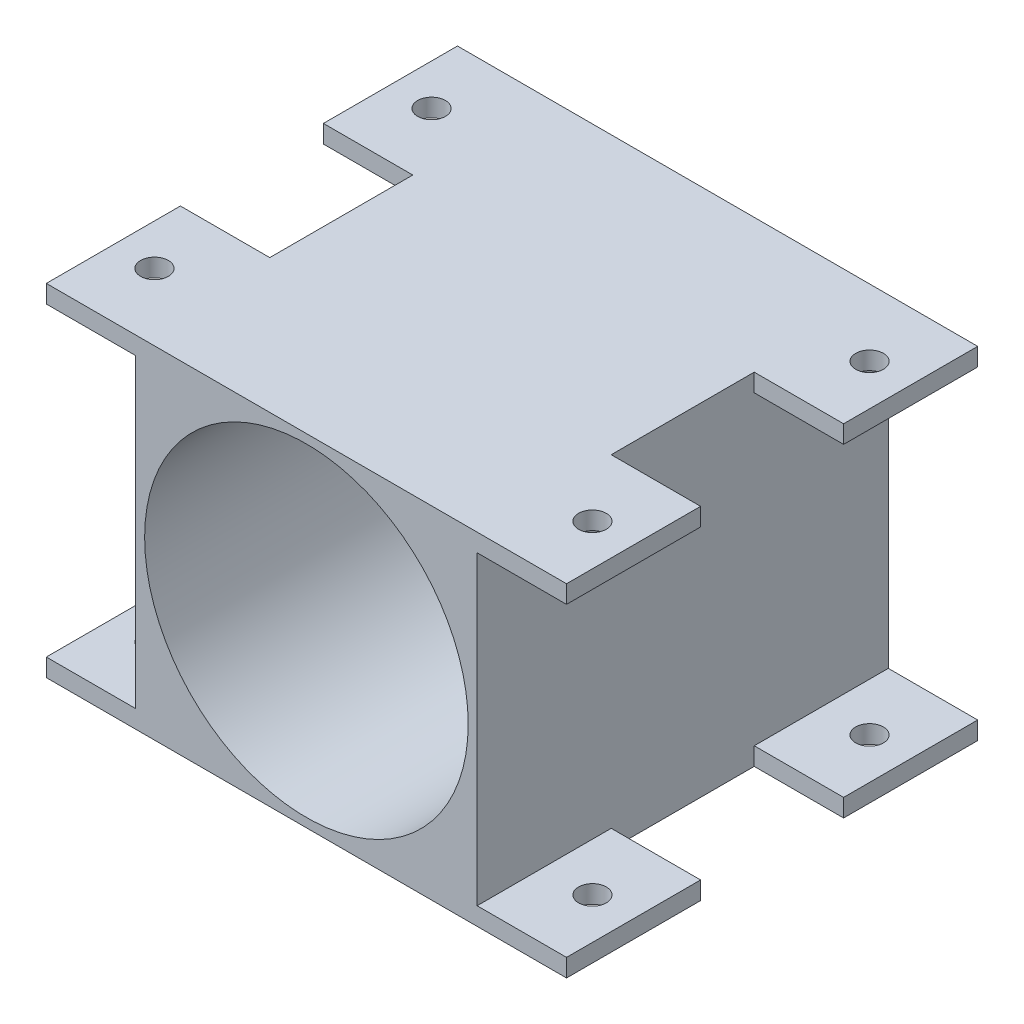
SolidWorks part; units mm, degrees
ref_plane "Front Plane" through (0, 0, 0) normal (0, 0, 1) x (1, 0, 0)
ref_plane "Top Plane" through (0, 0, 0) normal (0, 1, 0) x (1, 0, 0)
ref_plane "Right Plane" through (0, 0, 0) normal (1, 0, 0) x (0, 0, -1)
sketch "Sketch1" plane through (0, 0, 0) normal (0, 0, 1) x (1, 0, 0)
  circle A0 centre (0, 0) radius 18.1
  circle A1 centre (0, 0) radius 18.1
  circle A2 centre (-7.5, -12.9904) radius 1.55
  circle A3 centre (0, 0) radius 18.1
  circle A4 centre (7.5, -12.9904) radius 1.55
  circle A5 centre (-15, 0) radius 1.55
  circle A6 centre (0, 0) radius 18.1
  circle A7 centre (0, 6) radius 6.05
  circle A8 centre (-7.5, 12.9904) radius 1.55
  circle A9 centre (0, 0) radius 18.1
  circle A10 centre (7.5, 12.9904) radius 1.55
  circle A11 centre (0, 0) radius 18.1
  circle A12 centre (15, 0) radius 1.55
  point P24 (0, 0)
  dimension "D1" = 12.1
  dimension "D2" = 6
  dimension "D3" = 36.2
  dimension "D5" = 6
  dimension "D6" = 3.1
  dimension "D4" = 15
extrude "Boss-Extrude1" add sketch "Sketch1" along normal blind 1 contours A0 A12 A10 A8 A7 A5 A4 A2
sketch "Sketch2" plane through (0, 0, 0) normal (0, 0, -1) x (-1, 0, 0)
  line L0 (27.4238, 0) -> (-29.9497, 0) construction
  line L1 (0, 21.1091) -> (0, -19.3771) construction
  line L2 (19.1, 19.1) -> (19.1, -19.1)
  line L3 (19.1, -19.1) -> (-19.1, -19.1)
  line L4 (-19.1, 19.1) -> (-19.1, -19.1)
  line L5 (19.1, 19.1) -> (-19.1, 19.1)
  circle A1 centre (0, 0) radius 18.1 construction
  circle A2 centre (0, 0) radius 18.1
  point P9 (0, -19.1)
  point P11 (-19.1, 0)
  point P12 (19.1, 0)
  dimension "D2" = 19.1
  dimension "D1" = 19.1
extrude "Boss-Extrude2" add sketch "Sketch2" against normal blind 46
sketch "Sketch3" plane through (0, -19.1, 0) normal (0, -1, 0) x (1, 0, 0)
  line L0 (0, -11.2133) -> (0, 51.8698) construction
  line L1 (19.1, 0) -> (29.1, 0)
  line L2 (29.1, 0) -> (29.1, 15)
  line L3 (29.1, 15) -> (19.1, 15)
  line L4 (19.1, 46) -> (19.1, 0) construction
  line L5 (19.1, 46) -> (29.1, 46)
  line L6 (29.1, 46) -> (29.1, 31)
  line L7 (29.1, 31) -> (19.1, 31)
  line L8 (19.1, 31) -> (19.1, 46)
  line L9 (19.1, 15) -> (19.1, 0)
  line L10 (-19.1, 31) -> (-19.1, 46)
  line L11 (-19.1, 46) -> (-29.1, 46)
  line L12 (-29.1, 46) -> (-29.1, 31)
  line L13 (-29.1, 31) -> (-19.1, 31)
  line L14 (-29.1, 15) -> (-19.1, 15)
  line L15 (-29.1, 0) -> (-29.1, 15)
  line L16 (-19.1, 15) -> (-19.1, 0)
  line L17 (-19.1, 0) -> (-29.1, 0)
  circle A0 centre (24.5, 7.5) radius 1.55
  circle A1 centre (24.5, 38.5) radius 1.55
  circle A2 centre (-24.5, 38.5) radius 1.55
  circle A3 centre (-24.5, 7.5) radius 1.55
  dimension "D5" = 3.1
  dimension "D10" = 3.1
  dimension "D1" = 15
  dimension "D2" = 10
  dimension "D3" = 4.6
  dimension "D4" = 7.5
  dimension "D6" = 15
  dimension "D7" = 10
  dimension "D8" = 4.6
  dimension "D9" = 7.5
  dimension "D11" = 49
extrude "Boss-Extrude3" add sketch "Sketch3" against normal blind 2
mirror "Mirror1" about plane through (0, 0, 0) normal (0, 1, 0) of "Boss-Extrude3"
